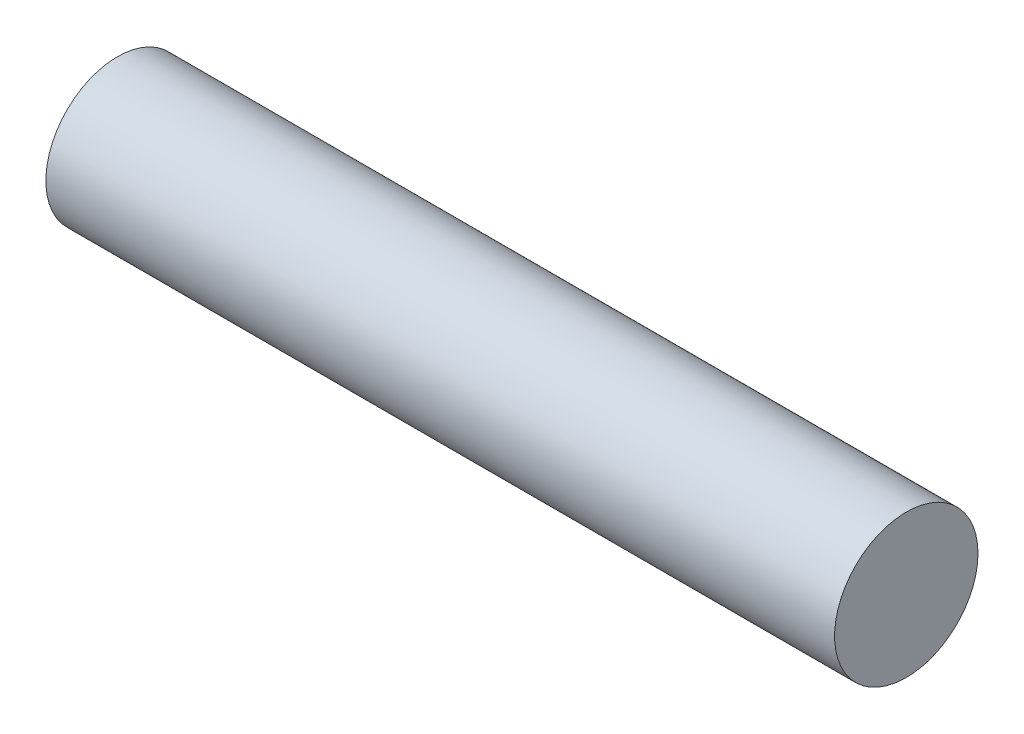
SolidWorks part; units mm, degrees
material "AISI 304"
ref_plane "Front Plane" through (0, 0, 0) normal (0, 0, 1) x (1, 0, 0)
ref_plane "Top Plane" through (0, 0, 0) normal (0, 1, 0) x (1, 0, 0)
ref_plane "Right Plane" through (0, 0, 0) normal (1, 0, 0) x (0, 0, -1)
sketch "Schizzo1" plane through (0, 0, 0) normal (1, 0, 0) x (0, 0, -1)
  circle A0 centre (0, 0) radius 2
  dimension "D1" = 4
extrude "Estrusione-Estrusione1" add sketch "Schizzo1" along normal blind 22
